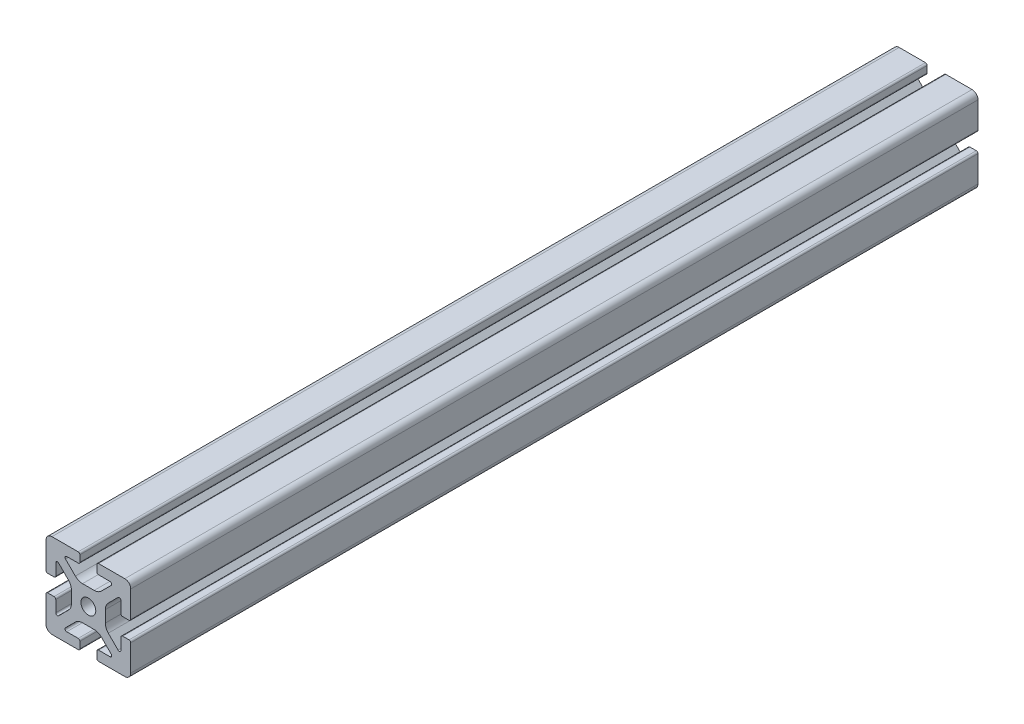
SolidWorks part; units mm, degrees
material "6061-T6 (SS)"
ref_plane "Front Plane" through (0, 0, 0) normal (0, 0, 1) x (1, 0, 0)
ref_plane "Top Plane" through (0, 0, 0) normal (0, 1, 0) x (1, 0, 0)
ref_plane "Right Plane" through (0, 0, 0) normal (1, 0, 0) x (0, 0, -1)
sketch "Sketch2" plane through (0, 0, 0) normal (0, 0, 1) x (1, 0, 0)
  line L0 (0, 20) -> (0, -20) construction
  line L1 (-20, 0) -> (20, 0) construction
  line L2 (4, -20) -> (20, -20)
  line L3 (20, -20) -> (20, -4)
  line L4 (4, -20) -> (4, -15.3907)
  line L5 (4, -15.3907) -> (12.1314, -15.3907)
  line L6 (12.1314, -15.3907) -> (4.7407, -8)
  line L7 (0, 0) -> (20, -20) construction
  line L8 (20, -4) -> (15.3907, -4)
  line L9 (15.3907, -4) -> (15.3907, -12.1314)
  line L10 (15.3907, -12.1314) -> (8, -4.7407)
  line L11 (11.6953, -8.436) -> (8.436, -11.6953) construction
  circle A0 centre (0, 0) radius 3.5
  arc A1 (10.2, -15.3907) -> (10.7657, -14.025) centre (10.2, -14.5907) ccw construction
  point P8 (0, -8)
  point P16 (10.0657, -10.0657)
  dimension "Center Hole Diameter" = 7
  dimension "D3" = 0.8
  dimension "Rail Height" = 40
  dimension "Rail Width" = 40
  dimension "T-Slot Width" = 8
  dimension "Slot Depth" = 12
  dimension "Slot Inner Width" = 22
sketch "Sketch3" plane through (0, 0, 0) normal (1, 0, 0) x (0, 0, -1)
  line L0 (-152.4, -20) -> (152.4, -20) construction
  line L1 (-127, 0) -> (127, 0) construction
  line L2 (0, 20) -> (0, -20) construction
  line L3 (0, 20) -> (0, -20) construction
  point P6 (-127, 0)
  point P8 (127, 0)
  dimension "Length" = 304.8
  dimension "D1" = 25.4
sketch "Sketch4" plane through (0, 0, 0) normal (0, 0, 1) x (1, 0, 0)
  line L0 (4.8, -20) -> (17.2, -20)
  line L1 (4, -20) -> (20, -20) construction
  line L2 (4, -20) -> (4, -15.3907) construction
  line L3 (4, -15.3907) -> (12.1314, -15.3907) construction
  line L4 (4, -16.1907) -> (4, -19.2)
  line L5 (4.8, -15.3907) -> (10.2, -15.3907)
  line L6 (0, -8) -> (2.7525, -8)
  line L7 (12.1314, -15.3907) -> (4.7407, -8) construction
  line L8 (6.1466, -9.4059) -> (10.7657, -14.025)
  line L9 (20, -20) -> (20, -4) construction
  line L10 (15.3907, -12.1314) -> (8, -4.7407) construction
  line L11 (15.3907, -4) -> (15.3907, -12.1314) construction
  line L12 (15.3907, -10.2) -> (15.3907, -4.8)
  line L13 (20, -4) -> (15.3907, -4) construction
  line L14 (16.1907, -4) -> (19.2, -4)
  line L15 (20, -4.8) -> (20, -17.2)
  line L16 (14.025, -10.7657) -> (9.4059, -6.1466)
  line L17 (8, 0) -> (8, -2.7525)
  line L18 (-20, 0) -> (20, 0) construction
  line L19 (0, -8) -> (0, -3.5)
  line L20 (0, 20) -> (0, -20) construction
  line L21 (8, 0) -> (3.5, 0)
  arc A0 (4, -19.2) -> (4.8, -20) centre (4.8, -19.2) ccw
  arc A1 (10.2, -15.3907) -> (10.7657, -14.025) centre (10.2, -14.5907) ccw construction
  arc A2 (4, -16.1907) -> (4.8, -15.3907) centre (4.8, -16.1907) cw
  arc A3 (10.2, -15.3907) -> (10.7657, -14.025) centre (10.2, -14.5907) ccw
  arc A4 (2.7525, -8) -> (6.1466, -9.4059) centre (2.7525, -12.8) cw
  arc A5 (17.2, -20) -> (20, -17.2) centre (17.2, -17.2) ccw
  arc A6 (14.025, -10.7657) -> (15.3907, -10.2) centre (14.5907, -10.2) ccw
  arc A7 (15.3907, -4.8) -> (16.1907, -4) centre (16.1907, -4.8) cw
  arc A8 (19.2, -4) -> (20, -4.8) centre (19.2, -4.8) cw
  arc A9 (9.4059, -6.1466) -> (8, -2.7525) centre (12.8, -2.7525) cw
  circle A10 centre (0, 0) radius 3.5 construction
  arc A11 (0, -3.5) -> (3.5, 0) centre (0, 0) ccw
  dimension "D1" = 2.8
  dimension "D2" = 4.8
extrude "Boss-Extrude1" add sketch "Sketch4" along normal mid plane 400
mirror "Mirror1" about plane through (0, 0, 0) normal (1, 0, 0) of bodies 134
mirror "Mirror2" about plane through (0, 0, 0) normal (0, 1, 0) of bodies 135
equation "\"D3@Sketch2\"=\"T-Slot Width@Sketch2\"*0.1"
equation "\"D1@Sketch4\"=\"D3@Sketch2\"*3.5"
equation "\"D2@Sketch4\"=\"D3@Sketch2\"*6"
equation "\"D1@Boss-Extrude1\"=\"Length@Sketch3\""
